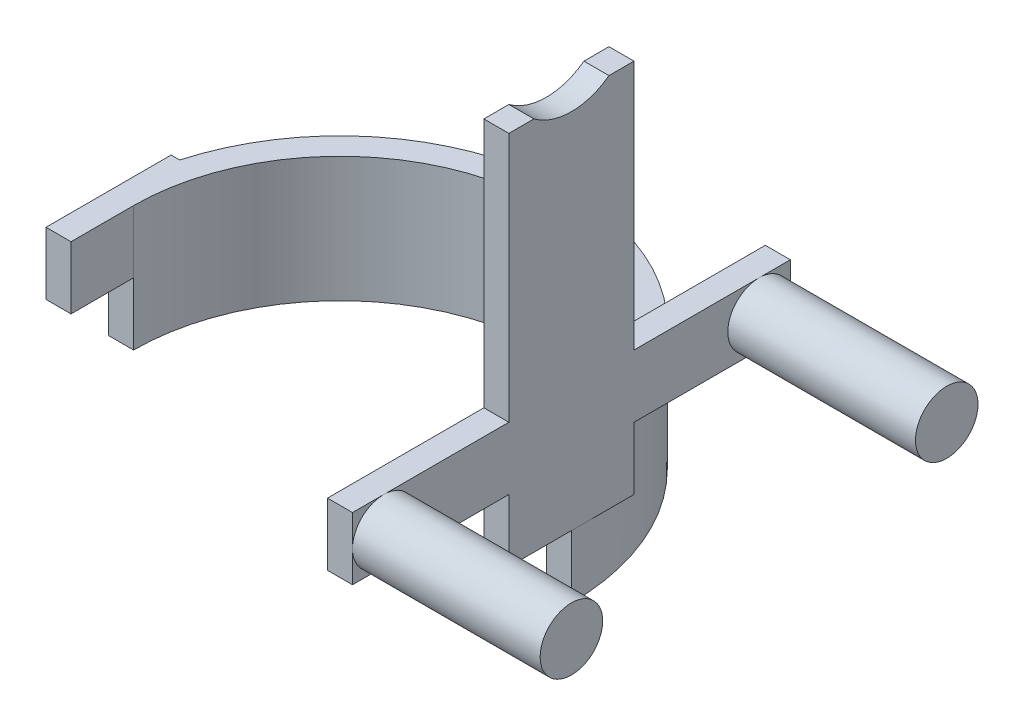
SolidWorks part; units mm, degrees
ref_plane "Front" through (0, 0, 0) normal (0, 0, 1) x (1, 0, 0)
ref_plane "Top" through (0, 0, 0) normal (0, 1, 0) x (1, 0, 0)
ref_plane "Right" through (0, 0, 0) normal (1, 0, 0) x (0, 0, -1)
sketch "草图1" plane through (0, 0, 0) normal (0, 1, 0) x (1, 0, 0)
  line L0 (-72.3418, 0) -> (74, 0) construction
  line L1 (0, 74) -> (0, -74) construction
  line L3 (-74, 20) -> (-71.2461, 20)
  line L4 (-74, 20) -> (-74, -20)
  line L5 (-74, -20) -> (-66, -20)
  line L6 (-66, 0) -> (-66, -20)
  line L7 (74, 20) -> (71.2461, 20)
  line L8 (74, 20) -> (74, -20)
  line L9 (74, -20) -> (66, -20)
  line L10 (66, 0) -> (66, -20)
  arc A0 (71.2461, 20) -> (-71.2461, 20) centre (0, 0) ccw
  arc A1 (66, 0) -> (-66, 0) centre (0, 0) ccw
  dimension "D1" = 40
  dimension "D2" = 20
  dimension "D3" = 8
  dimension "D4" = 8
  dimension "D6" = 40
  dimension "D7" = 20
extrude "凸台-拉伸1" add sketch "草图1" along normal blind 40
sketch "草图2" plane through (0, 40, 0) normal (0, 1, 0) x (1, 0, 0)
  line L1 (-74, -20) -> (-66, -20)
  line L2 (-74, -20) -> (-74, 20)
  line L3 (-74, 20) -> (-66, 20)
  line L4 (-66, -20) -> (-66, 20)
  line L5 (66, -20) -> (74, -20)
  line L6 (66, -20) -> (66, 20)
  line L7 (66, 20) -> (74, 20)
  line L8 (74, -20) -> (74, 20)
  dimension "D1" = 8
extrude "凸台-拉伸2" add sketch "草图2" along normal blind 100
sketch "草图3" plane through (-74, 0, 0) normal (-1, 0, 0) x (0, 0, 1)
  line L0 (-20, 140) -> (20, 140) construction
  circle A0 centre (0, 156) radius 20
  dimension "D1" = 16
extrude "切除-拉伸1" cut sketch "草图3" against normal through all
sketch "草图4" plane through (-74, 0, 0) normal (-1, 0, 0) x (0, 0, 1)
  line L1 (-20, 40) -> (29.7839, 40)
  line L2 (-20, 40) -> (-20, 153.9823)
  line L3 (-20, 153.9823) -> (29.7839, 153.9823)
  line L4 (29.7839, 40) -> (29.7839, 153.9823)
extrude "切除-拉伸3" cut sketch "草图4" against normal blind 10
sketch "草图5" plane through (0, 0, 0) normal (0, -1, 0) x (1, 0, 0)
  line L0 (66, 0) -> (66, 20) construction
  line L1 (-71.2461, 20) -> (-66, 20)
  line L3 (-74, 0) -> (-66, 0)
  line L4 (-66, 20) -> (-66, 0)
  line L5 (71.2461, 20) -> (66, 20)
  line L7 (74, 0) -> (66, 0)
  line L8 (66, 20) -> (66, 0)
  arc A0 (-66, 0) -> (66, 0) centre (0, 0) ccw construction
  arc A1 (-74, 0) -> (74, 0) centre (0, 0) ccw
  circle A2 centre (0, 0) radius 84.7622
  arc A3 (71.2461, 20) -> (-71.2461, 20) centre (0, 0) ccw
extrude "切除-拉伸4" cut sketch "草图5" against normal blind 20
sketch "草图6" plane through (74, 0, 0) normal (1, 0, 0) x (0, 0, -1)
  line L0 (66, 40) -> (0, 40) construction
  line L1 (70, 40) -> (-70, 40)
  line L2 (70, 40) -> (70, 60)
  line L3 (70, 60) -> (-70, 60)
  line L4 (-70, 40) -> (-70, 60)
  line L5 (0, 0) -> (0, 148.7503) construction
  dimension "D1" = 140
  dimension "D2" = 70
  dimension "D3" = 20
extrude "凸台-拉伸3" add sketch "草图6" against normal blind 8
sketch "草图7" plane through (74, 0, 0) normal (1, 0, 0) x (0, 0, -1)
  circle A0 centre (-60, 50) radius 10
  circle A1 centre (60, 50) radius 10
extrude "凸台-拉伸4" add sketch "草图7" along normal blind 60
